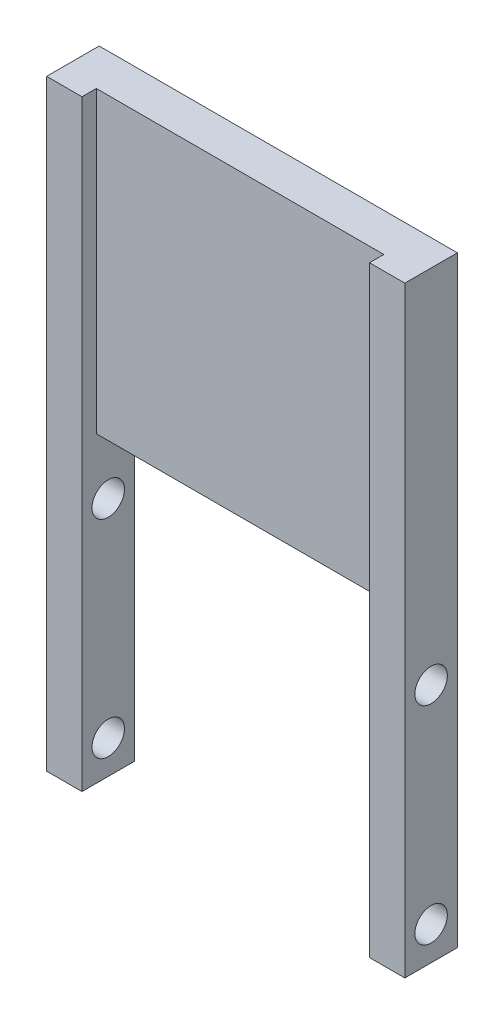
SolidWorks part; units mm, degrees
ref_plane "前视基准面" through (0, 0, 0) normal (0, 0, 1) x (1, 0, 0)
ref_plane "上视基准面" through (0, 0, 0) normal (0, 1, 0) x (1, 0, 0)
ref_plane "右视基准面" through (0, 0, 0) normal (1, 0, 0) x (0, 0, -1)
sketch "Sketch1" plane through (0, 0, 0) normal (0, 0, 1) x (1, 0, 0)
  line L0 (33.8, 0) -> (37.5, 0)
  line L1 (0, 0) -> (3.7, 0)
  line L2 (0, 0) -> (0, 63)
  line L3 (0, 63) -> (37.5, 63)
  line L4 (37.5, 0) -> (37.5, 63)
  line L6 (3.7, 0) -> (3.7, 31.7)
  line L7 (3.7, 31.7) -> (33.8, 31.7)
  line L8 (33.8, 0) -> (33.8, 31.7)
  dimension "D1" = 37.5
  dimension "D2" = 31.3
  dimension "D3" = 63
  dimension "D4" = 3.7
  dimension "D5" = 3.7
extrude "Boss-Extrude1" add sketch "Sketch1" against normal blind 5.5
sketch "Sketch2" plane through (0, 0, 0) normal (0, 0, 1) x (1, 0, 0)
  line L0 (37.5, 63) -> (0, 63) construction
  line L1 (3.7, 31.7) -> (33.8, 31.7)
  line L2 (3.7, 31.7) -> (3.7, 63)
  line L3 (3.7, 63) -> (33.8, 63)
  line L4 (33.8, 31.7) -> (33.8, 63)
  line L6 (33.8, 31.7) -> (33.8, 0) construction
extrude "Cut-Extrude1" cut sketch "Sketch2" against normal blind 1.5
sketch "Sketch3" plane through (37.5, 0, 0) normal (1, 0, 0) x (0, 0, -1)
  line L0 (2.75, 0) -> (2.75, 63) construction
  line L1 (5.5, 0) -> (0, 0) construction
  line L2 (5.5, 63) -> (0, 63) construction
  circle A0 centre (2.75, 3.5) radius 1.7
  circle A1 centre (2.75, 25.2) radius 1.7
  dimension "D1" = 3.4
  dimension "D2" = 3.5
  dimension "D3" = 3.4
  dimension "D4" = 21.7
extrude "Cut-Extrude2" cut sketch "Sketch3" against normal through all
